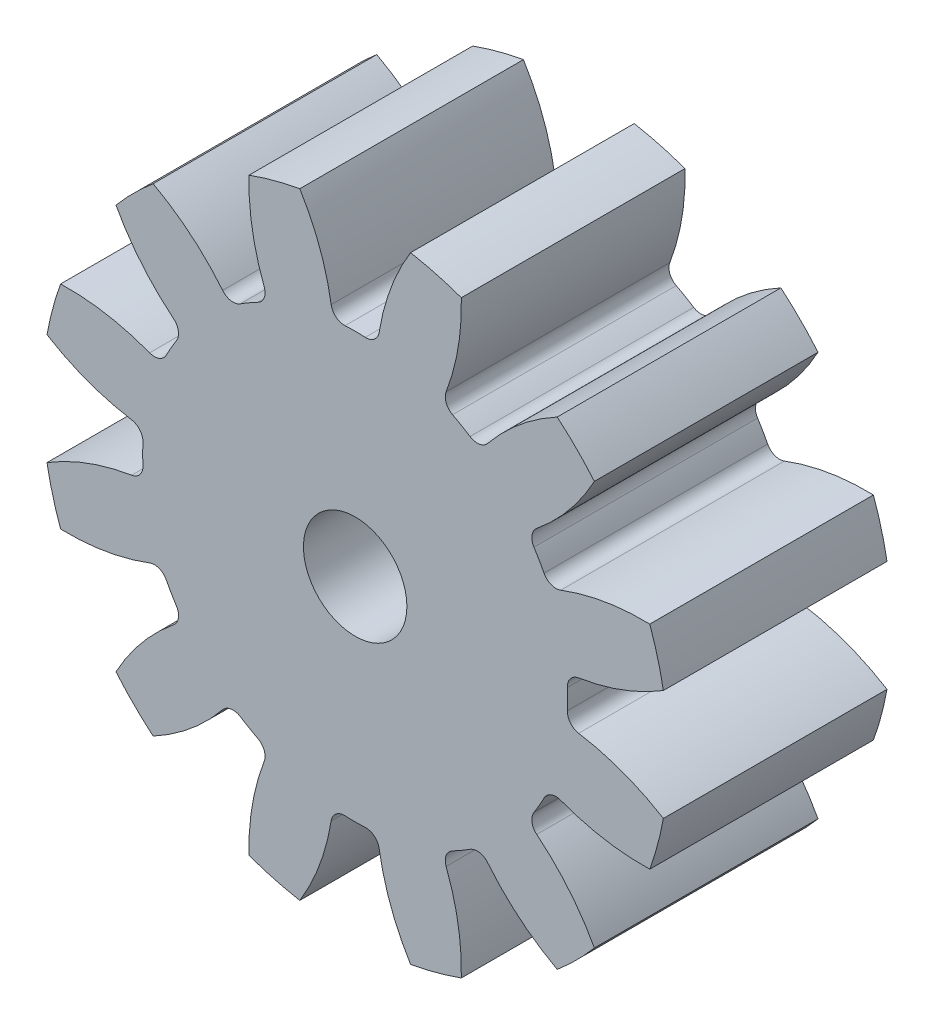
SolidWorks part; units mm, degrees
ref_plane "Front" through (0, 0, 0) normal (0, 0, 1) x (1, 0, 0)
ref_plane "Top" through (0, 0, 0) normal (0, 1, 0) x (1, 0, 0)
ref_plane "Right" through (0, 0, 0) normal (1, 0, 0) x (0, 0, -1)
sketch "Sketch2" plane through (0, 0, 0) normal (0, 0, 1) x (1, 0, 0)
  circle A0 centre (0, 0) radius 9.5
  circle A1 centre (0, 0) radius 12
  circle A2 centre (0, 0) radius 14
  dimension "D1" = 24
  dimension "D2" = 28
  dimension "D3" = 4.5
extrude "Boss-Extrude1" add sketch "Sketch2" along normal mid plane 10 contours A2
sketch "Sketch3" plane through (0, 0, 0) normal (0, 0, 1) x (1, 0, 0)
  line L0 (0, 0) -> (0, 14) construction
  line L1 (-1.5663, 11.8973) -> (1.5663, 11.8973) construction
  line L2 (0, 0) -> (-0.9997, 9.4472) construction
  line L3 (0, 7.5939) -> (-2.6122, 14.7708) construction
  line L4 (0, 0) -> (3.6235, 13.523) construction
  line L5 (1.5663, 11.8973) -> (4.5922, 11.0866) construction
  circle A0 centre (0, 0) radius 14 construction
  arc A1 (-0.9997, 9.4472) -> (-3.0957, 14.6771) centre (-11.2897, 8.3583) ccw
  arc A2 (0.9997, 9.4472) -> (3.0957, 14.6771) centre (11.2897, 8.3583) cw
  circle A3 centre (0, 0) radius 9.5 construction
  arc A4 (0.9997, 9.4472) -> (-0.9997, 9.4472) centre (0, 0) ccw
  circle A6 centre (0, 0) radius 12 construction
  circle A7 centre (0, 0) radius 15
  arc A8 (3.0957, 14.6771) -> (-3.0957, 14.6771) centre (0, 0) ccw
  circle A9 centre (0, 0) radius 14 construction
  dimension "D2" = 20
  dimension "D3" = 15
  dimension "D1" = 1
extrude "Cut-Extrude1" cut sketch "Sketch3" against normal through all both and the other way through all contours A8 A1 A4 A2
fillet "Fillet1" radius 0.6 2 edges at (0.9997, 9.4472, 0) (-0.9997, 9.4472, 0)
pattern_circular "CirPattern1" count 12 over 360 about axis through (0, 0, 0) along (0, 0, 1) of "Fillet1", "Cut-Extrude1"
sketch "Sketch4" plane through (0, 0, 5) normal (0, 0, 1) x (1, 0, 0)
  circle A0 centre (0, 0) radius 2.3125
  dimension "D1" = 4.625
extrude "Cut-Extrude2" cut sketch "Sketch4" against normal blind 3.5 contours A0
sketch "Sketch5" plane through (0, 0, -5) normal (0, 0, -1) x (-1, 0, 0)
  circle A0 centre (0, 0) radius 1.25
  dimension "D1" = 2.5
extrude "Cut-Extrude3" cut sketch "Sketch5" against normal through all
equation "\"teeth\"= 12"
equation "\"module\"= 2mm"
equation "\"D1@Sketch2\"=\"module\"*\"teeth\""
equation "\"D2@Sketch2\"=(\"teeth\"+2)*\"module\""
equation "\"pressure_angle\"= 20deg"
equation "\"D2@Sketch3\"=\"pressure_angle\""
equation "\"D3@Sketch3\"=180/\"teeth\""
equation "\"D1@Fillet1\"=0.3 * \"module\""
equation "\"D1@CirPattern1\"=\"teeth\""
equation "\"D3@Sketch2\"=\"module\" * if ( \"module\" >= 1.25 , 2.25 , 2.4 )"
